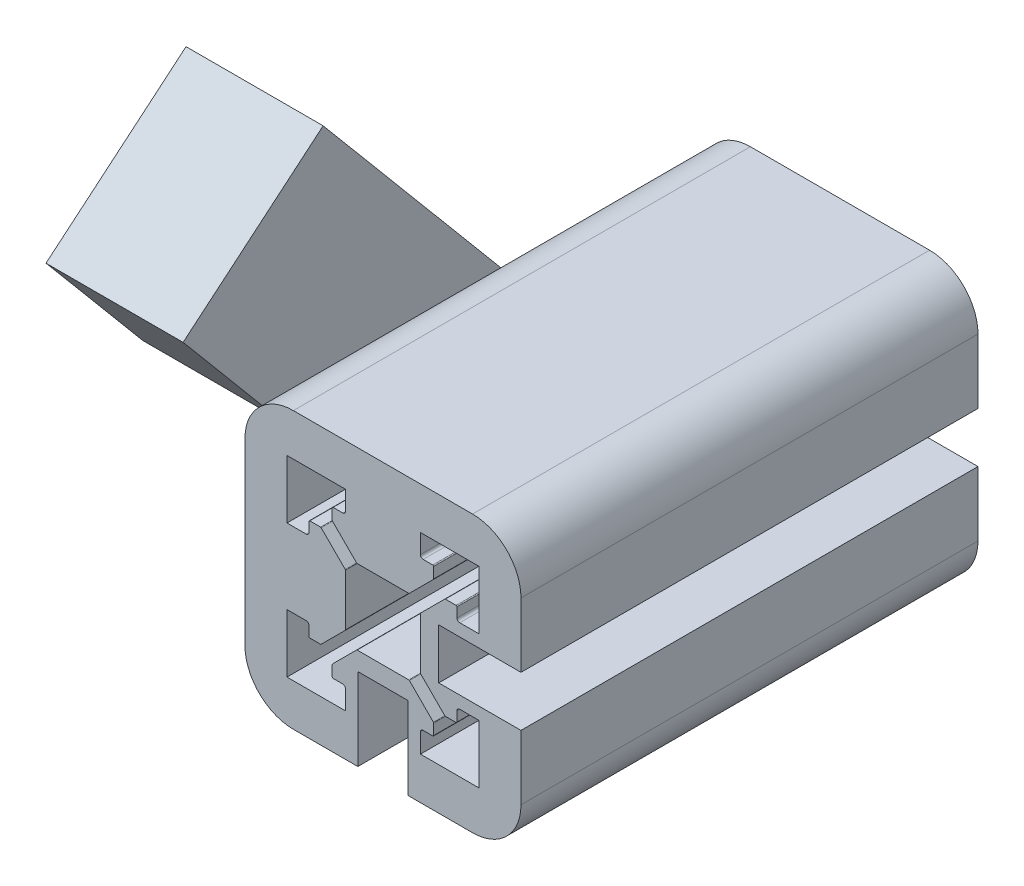
SolidWorks part; units mm, degrees
ref_plane "Ön Düzlem" through (0, 0, 0) normal (0, 0, 1) x (1, 0, 0)
ref_plane "Üst Düzlem" through (0, 0, 0) normal (0, 1, 0) x (1, 0, 0)
ref_plane "Sağ Düzlem" through (0, 0, 0) normal (1, 0, 0) x (0, 0, -1)
sketch "Çizim6" plane through (0, 0, 0) normal (0, 0, 1) x (1, 0, 0)
  line L5 (-115.3715, 18.9738) -> (-110.3715, 18.9738)
  line L6 (-115.3715, 13.4738) -> (-110.3715, 13.4738)
  line L64 (-135.0715, 20.3238) -> (-133.8715, 20.3238)
  line L65 (-133.5715, 20.6238) -> (-133.5715, 21.6738)
  line L66 (-133.4715, 21.7738) -> (-132.3044, 21.7738)
  line L67 (-132.2336, 21.7445) -> (-129.6008, 19.1116)
  line L68 (-129.5715, 19.0409) -> (-129.5715, 13.4066)
  line L69 (-132.2336, 10.7031) -> (-129.6008, 13.3359)
  line L70 (-133.4715, 10.6738) -> (-132.3044, 10.6738)
  line L71 (-133.5715, 11.8238) -> (-133.5715, 10.7738)
  line L72 (-135.0715, 12.1238) -> (-133.8715, 12.1238)
  line L79 (-129.5715, 6.6238) -> (-129.5715, 7.8238)
  line L80 (-129.8715, 8.1238) -> (-130.9215, 8.1238)
  line L81 (-131.0215, 8.2238) -> (-131.0215, 9.3909)
  line L82 (-130.9922, 9.4616) -> (-128.3594, 12.0945)
  line L83 (-128.2887, 12.1238) -> (-122.6544, 12.1238)
  line L84 (-119.9508, 9.4616) -> (-122.5836, 12.0945)
  line L85 (-119.9215, 8.2238) -> (-119.9215, 9.3909)
  line L86 (-121.0715, 8.1238) -> (-120.0215, 8.1238)
  line L87 (-121.3715, 6.6238) -> (-121.3715, 7.8238)
  line L94 (-115.8715, 12.1238) -> (-117.0715, 12.1238)
  line L95 (-117.3715, 11.8238) -> (-117.3715, 10.7738)
  line L96 (-117.4715, 10.6738) -> (-118.6387, 10.6738)
  line L97 (-118.7094, 10.7031) -> (-121.3422, 13.3359)
  line L98 (-121.3715, 13.4066) -> (-121.3715, 19.0409)
  line L99 (-118.7094, 21.7445) -> (-121.3422, 19.1116)
  line L100 (-117.4715, 21.7738) -> (-118.6387, 21.7738)
  line L101 (-117.3715, 20.6238) -> (-117.3715, 21.6738)
  line L102 (-115.8715, 20.3238) -> (-117.0715, 20.3238)
  line L109 (-121.3715, 25.8238) -> (-121.3715, 24.6238)
  line L110 (-121.0715, 24.3238) -> (-120.0215, 24.3238)
  line L111 (-119.9215, 24.2238) -> (-119.9215, 23.0566)
  line L112 (-119.9508, 22.9859) -> (-122.5836, 20.3531)
  line L113 (-122.6544, 20.3238) -> (-128.2887, 20.3238)
  line L114 (-130.9922, 22.9859) -> (-128.3594, 20.3531)
  line L115 (-131.0215, 24.2238) -> (-131.0215, 23.0566)
  line L116 (-129.8715, 24.3238) -> (-130.9215, 24.3238)
  line L117 (-129.5715, 25.8238) -> (-129.5715, 24.6238)
  line L122 (-119.3715, 18.9738) -> (-115.3715, 18.9738)
  line L123 (-119.3715, 13.4738) -> (-115.3715, 13.4738)
  line L126 (-119.3715, 18.9738) -> (-119.3715, 13.4738)
  line L128 (-122.7215, 10.1238) -> (-122.7215, 6.1238)
  line L129 (-122.7215, 10.1238) -> (-128.2215, 10.1238)
  line L130 (-128.2215, 10.1238) -> (-128.2215, 6.1238)
  line L142 (-135.0715, 20.3238) -> (-135.8715, 20.3238)
  line L143 (-135.0715, 12.1238) -> (-135.5715, 12.1238)
  line L144 (-129.5715, 6.6238) -> (-129.5715, 6.1238)
  line L145 (-129.5715, 25.8238) -> (-129.5715, 26.6238)
  line L146 (-121.3715, 25.8238) -> (-121.3715, 26.3238)
  line L147 (-115.8715, 20.3238) -> (-115.3715, 20.3238)
  line L148 (-115.8715, 12.1238) -> (-115.3715, 12.1238)
  line L149 (-121.3715, 6.6238) -> (-121.3715, 6.1238)
  line L150 (-135.2715, 31.3238) -> (-130.0215, 31.3238)
  line L151 (-130.0215, 31.3238) -> (-128.2215, 31.3238)
  line L152 (-125.4715, 31.3238) -> (-125.4715, 31.3238)
  line L153 (-125.4715, 31.3238) -> (-125.4715, 31.3238)
  line L154 (-125.4715, 31.3238) -> (-125.4715, 31.3238)
  line L155 (-120.9215, 31.3238) -> (-122.7215, 31.3238)
  line L156 (-120.9215, 31.3238) -> (-115.6715, 31.3238)
  line L157 (-110.3715, 20.7738) -> (-110.3715, 26.0238)
  line L158 (-110.3715, 20.7738) -> (-110.3715, 18.9738)
  line L159 (-110.3715, 16.2238) -> (-110.3715, 16.2238)
  line L160 (-110.3715, 16.2238) -> (-110.3715, 16.2238)
  line L161 (-110.3715, 16.2238) -> (-110.3715, 16.2238)
  line L162 (-110.3715, 11.6738) -> (-110.3715, 13.4738)
  line L163 (-110.3715, 6.4238) -> (-110.3715, 11.6738)
  line L164 (-120.9215, 1.1238) -> (-115.6715, 1.1238)
  line L165 (-120.9215, 1.1238) -> (-122.7215, 1.1238)
  line L166 (-125.4715, 1.1238) -> (-125.4715, 1.1238)
  line L167 (-125.4715, 1.1238) -> (-125.4715, 1.1238)
  line L168 (-125.4715, 1.1238) -> (-125.4715, 1.1238)
  line L169 (-130.0215, 1.1238) -> (-128.2215, 1.1238)
  line L170 (-135.2715, 1.1238) -> (-130.0215, 1.1238)
  line L171 (-140.5715, 6.4238) -> (-140.5715, 11.6738)
  line L172 (-140.5715, 11.6738) -> (-140.5715, 16.2238)
  line L173 (-140.5715, 16.2238) -> (-140.5715, 16.2238)
  line L174 (-140.5715, 16.2238) -> (-140.5715, 16.2238)
  line L175 (-140.5715, 16.2238) -> (-140.5715, 16.2238)
  line L176 (-140.5715, 20.7738) -> (-140.5715, 16.2238)
  line L177 (-140.5715, 20.7738) -> (-140.5715, 26.0238)
  line L178 (-135.5715, 20.7738) -> (-135.5715, 26.0238) construction
  line L179 (-135.2715, 26.3238) -> (-130.0215, 26.3238) construction
  line L180 (-115.3715, 20.7738) -> (-115.3715, 26.0238) construction
  line L181 (-120.9215, 26.3238) -> (-115.6715, 26.3238) construction
  line L182 (-115.3715, 20.7738) -> (-115.3715, 18.9738) construction
  line L183 (-115.3715, 6.4238) -> (-115.3715, 11.6738) construction
  line L184 (-120.9215, 6.1238) -> (-115.6715, 6.1238) construction
  line L185 (-115.3715, 11.6738) -> (-115.3715, 13.4738) construction
  line L186 (-120.9215, 6.1238) -> (-122.7215, 6.1238) construction
  line L187 (-120.9215, 26.3238) -> (-122.7215, 26.3238) construction
  line L188 (-130.0215, 26.3238) -> (-128.2215, 26.3238) construction
  line L189 (-135.5715, 20.7738) -> (-135.5715, 18.9738) construction
  line L190 (-135.5715, 11.6738) -> (-135.5715, 13.4738) construction
  line L191 (-135.5715, 6.4238) -> (-135.5715, 11.6738) construction
  line L192 (-135.2715, 6.1238) -> (-130.0215, 6.1238) construction
  line L193 (-130.0215, 6.1238) -> (-128.2215, 6.1238) construction
  line L194 (-122.7215, 6.1238) -> (-122.7215, 1.1238)
  line L195 (-128.2215, 6.1238) -> (-128.2215, 1.1238)
  line L196 (-135.8715, 20.3238) -> (-135.9715, 20.3238)
  line L197 (-135.9715, 20.2238) -> (-135.9715, 26.7238) construction
  line L198 (-122.7215, 31.3238) -> (-128.2215, 31.3238)
  line L204 (-110.3715, 20.7738) -> (-110.3715, 16.2238) construction
  line L205 (-110.3715, 11.6738) -> (-110.3715, 16.2238) construction
  line L206 (-120.9215, 31.3238) -> (-125.4715, 31.3238) construction
  line L207 (-130.0215, 31.3238) -> (-125.4715, 31.3238) construction
  line L208 (-120.9215, 1.1238) -> (-125.4715, 1.1238) construction
  line L209 (-130.0215, 1.1238) -> (-125.4715, 1.1238) construction
  line L210 (-131.5715, 13.4738) -> (-135.5715, 13.4738) [skipped]
  line L211 (-131.5715, 13.4738) -> (-135.5715, 13.4738) construction
  line L212 (-131.5715, 13.4738) -> (-131.5715, 18.9738) [skipped]
  line L213 (-131.5715, 13.4738) -> (-131.5715, 18.9738) construction
  line L214 (-131.5715, 18.9738) -> (-135.5715, 18.9738) [skipped]
  line L215 (-131.5715, 18.9738) -> (-135.5715, 18.9738) construction
  line L216 (-129.5715, 26.6238) -> (-129.5715, 26.7238)
  line L217 (-135.9715, 26.7238) -> (-129.4715, 26.7238) construction
  line L218 (-114.9715, 26.7238) -> (-114.9715, 20.3238)
  line L219 (-121.3715, 26.7238) -> (-114.9715, 26.7238)
  line L220 (-114.9715, 5.7238) -> (-121.3715, 5.7238)
  line L221 (-114.9715, 12.1238) -> (-114.9715, 5.7238)
  line L222 (-135.9715, 5.7238) -> (-135.9715, 12.1238)
  line L223 (-129.5715, 5.7238) -> (-135.9715, 5.7238)
  line L224 (-121.3715, 6.1238) -> (-121.3715, 5.7238)
  line L225 (-115.3715, 12.1238) -> (-114.9715, 12.1238)
  line L226 (-129.5715, 6.1238) -> (-129.5715, 5.7238)
  line L227 (-135.9715, 20.3238) -> (-135.9715, 26.7238)
  line L228 (-135.9715, 26.7238) -> (-129.5715, 26.7238)
  line L229 (-135.5715, 12.1238) -> (-135.9715, 12.1238)
  line L230 (-121.3715, 26.3238) -> (-121.3715, 26.7238)
  line L231 (-115.3715, 20.3238) -> (-114.9715, 20.3238)
  line L240 (-121.4715, 25.8238) -> (-121.4715, 26.3238) construction
  line L241 (-121.4715, 25.8238) -> (-121.4715, 24.6238) construction
  line L242 (-121.0715, 24.2238) -> (-120.0215, 24.2238) construction
  line L243 (-120.0215, 24.2238) -> (-120.0215, 23.0566) construction
  line L244 (-120.0215, 23.0566) -> (-122.6544, 20.4238) construction
  line L245 (-122.6544, 20.4238) -> (-128.2887, 20.4238) construction
  line L246 (-130.9215, 23.0566) -> (-128.2887, 20.4238) construction
  line L247 (-130.9215, 24.2238) -> (-130.9215, 23.0566) construction
  line L248 (-129.8715, 24.2238) -> (-130.9215, 24.2238) construction
  line L249 (-129.4715, 25.8238) -> (-129.4715, 24.6238) construction
  line L250 (-129.4715, 25.8238) -> (-129.4715, 26.7238) construction
  line L251 (-135.8715, 26.6238) -> (-129.5715, 26.6238) construction
  line L252 (-135.8715, 20.3238) -> (-135.8715, 26.6238) construction
  line L253 (-135.0715, 20.2238) -> (-135.9715, 20.2238) construction
  line L254 (-135.0715, 20.2238) -> (-133.8715, 20.2238) construction
  line L255 (-133.4715, 20.6238) -> (-133.4715, 21.6738) construction
  line L256 (-133.4715, 21.6738) -> (-132.3044, 21.6738) construction
  line L257 (-132.3044, 21.6738) -> (-129.6715, 19.0409) construction
  line L258 (-129.6715, 19.0409) -> (-129.6715, 13.4066) construction
  line L259 (-132.3044, 10.7738) -> (-129.6715, 13.4066) construction
  line L260 (-133.4715, 10.7738) -> (-132.3044, 10.7738) construction
  line L261 (-133.4715, 11.8238) -> (-133.4715, 10.7738) construction
  line L262 (-135.0715, 12.2238) -> (-133.8715, 12.2238) construction
  line L263 (-135.0715, 12.2238) -> (-135.5715, 12.2238) construction
  line L264 (-128.2215, 22.3238) -> (-128.2215, 26.3238) [skipped]
  line L265 (-128.2215, 22.3238) -> (-128.2215, 26.3238) construction
  line L266 (-128.2215, 22.3238) -> (-122.7215, 22.3238) [skipped]
  line L267 (-128.2215, 22.3238) -> (-122.7215, 22.3238) construction
  line L268 (-122.7215, 22.3238) -> (-122.7215, 26.3238) [skipped]
  line L269 (-122.7215, 22.3238) -> (-122.7215, 26.3238) construction
  arc A46 (-133.8715, 20.3238) -> (-133.5715, 20.6238) centre (-133.8715, 20.6238) ccw
  arc A47 (-133.5715, 21.6738) -> (-133.4715, 21.7738) centre (-133.4715, 21.6738) cw
  arc A48 (-132.2336, 21.7445) -> (-132.3044, 21.7738) centre (-132.3044, 21.6738) ccw
  arc A49 (-129.5715, 19.0409) -> (-129.6008, 19.1116) centre (-129.6715, 19.0409) ccw
  arc A50 (-129.5715, 13.4066) -> (-129.6008, 13.3359) centre (-129.6715, 13.4066) cw
  arc A51 (-132.2336, 10.7031) -> (-132.3044, 10.6738) centre (-132.3044, 10.7738) cw
  arc A52 (-133.4715, 10.6738) -> (-133.5715, 10.7738) centre (-133.4715, 10.7738) cw
  arc A53 (-133.5715, 11.8238) -> (-133.8715, 12.1238) centre (-133.8715, 11.8238) ccw
  arc A57 (-129.5715, 7.8238) -> (-129.8715, 8.1238) centre (-129.8715, 7.8238) ccw
  arc A58 (-130.9215, 8.1238) -> (-131.0215, 8.2238) centre (-130.9215, 8.2238) cw
  arc A59 (-130.9922, 9.4616) -> (-131.0215, 9.3909) centre (-130.9215, 9.3909) ccw
  arc A60 (-128.2887, 12.1238) -> (-128.3594, 12.0945) centre (-128.2887, 12.0238) ccw
  arc A61 (-122.6544, 12.1238) -> (-122.5836, 12.0945) centre (-122.6544, 12.0238) cw
  arc A62 (-119.9508, 9.4616) -> (-119.9215, 9.3909) centre (-120.0215, 9.3909) cw
  arc A63 (-119.9215, 8.2238) -> (-120.0215, 8.1238) centre (-120.0215, 8.2238) cw
  arc A64 (-121.0715, 8.1238) -> (-121.3715, 7.8238) centre (-121.0715, 7.8238) ccw
  arc A68 (-117.0715, 12.1238) -> (-117.3715, 11.8238) centre (-117.0715, 11.8238) ccw
  arc A69 (-117.3715, 10.7738) -> (-117.4715, 10.6738) centre (-117.4715, 10.7738) cw
  arc A70 (-118.7094, 10.7031) -> (-118.6387, 10.6738) centre (-118.6387, 10.7738) ccw
  arc A71 (-121.3715, 13.4066) -> (-121.3422, 13.3359) centre (-121.2715, 13.4066) ccw
  arc A72 (-121.3715, 19.0409) -> (-121.3422, 19.1116) centre (-121.2715, 19.0409) cw
  arc A73 (-118.7094, 21.7445) -> (-118.6387, 21.7738) centre (-118.6387, 21.6738) cw
  arc A74 (-117.4715, 21.7738) -> (-117.3715, 21.6738) centre (-117.4715, 21.6738) cw
  arc A75 (-117.3715, 20.6238) -> (-117.0715, 20.3238) centre (-117.0715, 20.6238) ccw
  arc A79 (-121.3715, 24.6238) -> (-121.0715, 24.3238) centre (-121.0715, 24.6238) ccw
  arc A80 (-120.0215, 24.3238) -> (-119.9215, 24.2238) centre (-120.0215, 24.2238) cw
  arc A81 (-119.9508, 22.9859) -> (-119.9215, 23.0566) centre (-120.0215, 23.0566) ccw
  arc A82 (-122.6544, 20.3238) -> (-122.5836, 20.3531) centre (-122.6544, 20.4238) ccw
  arc A83 (-128.2887, 20.3238) -> (-128.3594, 20.3531) centre (-128.2887, 20.4238) cw
  arc A84 (-130.9922, 22.9859) -> (-131.0215, 23.0566) centre (-130.9215, 23.0566) cw
  arc A85 (-131.0215, 24.2238) -> (-130.9215, 24.3238) centre (-130.9215, 24.2238) cw
  arc A86 (-129.8715, 24.3238) -> (-129.5715, 24.6238) centre (-129.8715, 24.6238) ccw
  arc A89 (-110.3715, 26.0238) -> (-115.6715, 31.3238) centre (-115.6715, 26.0238) ccw
  arc A90 (-115.6715, 1.1238) -> (-110.3715, 6.4238) centre (-115.6715, 6.4238) ccw
  arc A91 (-135.2715, 1.1238) -> (-140.5715, 6.4238) centre (-135.2715, 6.4238) cw
  arc A92 (-140.5715, 26.0238) -> (-135.2715, 31.3238) centre (-135.2715, 26.0238) cw
  arc A93 (-135.5715, 26.0238) -> (-135.2715, 26.3238) centre (-135.2715, 26.0238) cw construction
  arc A94 (-115.3715, 26.0238) -> (-115.6715, 26.3238) centre (-115.6715, 26.0238) ccw construction
  arc A95 (-115.6715, 6.1238) -> (-115.3715, 6.4238) centre (-115.6715, 6.4238) ccw construction
  arc A96 (-135.2715, 6.1238) -> (-135.5715, 6.4238) centre (-135.2715, 6.4238) cw construction
  arc A98 (-133.4715, 10.7738) -> (-133.4715, 10.7738) centre (-133.4715, 10.7738) cw
  arc A99 (-132.3044, 10.7738) -> (-132.3044, 10.7738) centre (-132.3044, 10.7738) cw
  arc A100 (-129.6715, 13.4066) -> (-129.6715, 13.4066) centre (-129.6715, 13.4066) cw
  arc A101 (-129.6715, 19.0409) -> (-129.6715, 19.0409) centre (-129.6715, 19.0409) ccw
  arc A102 (-132.3044, 21.6738) -> (-132.3044, 21.6738) centre (-132.3044, 21.6738) ccw
  arc A103 (-133.4715, 21.6738) -> (-133.4715, 21.6738) centre (-133.4715, 21.6738) cw
  arc A106 (-130.9215, 24.2238) -> (-130.9215, 24.2238) centre (-130.9215, 24.2238) cw
  arc A107 (-130.9215, 23.0566) -> (-130.9215, 23.0566) centre (-130.9215, 23.0566) cw
  arc A108 (-128.2887, 20.4238) -> (-128.2887, 20.4238) centre (-128.2887, 20.4238) cw
  arc A109 (-122.6544, 20.4238) -> (-122.6544, 20.4238) centre (-122.6544, 20.4238) ccw
  arc A110 (-120.0215, 23.0566) -> (-120.0215, 23.0566) centre (-120.0215, 23.0566) ccw
  arc A111 (-120.0215, 24.2238) -> (-120.0215, 24.2238) centre (-120.0215, 24.2238) cw
  arc A113 (-121.4715, 24.6238) -> (-121.0715, 24.2238) centre (-121.0715, 24.6238) ccw construction
  arc A114 (-129.8715, 24.2238) -> (-129.4715, 24.6238) centre (-129.8715, 24.6238) ccw construction
  arc A115 (-133.8715, 20.2238) -> (-133.4715, 20.6238) centre (-133.8715, 20.6238) ccw construction
  arc A116 (-133.4715, 11.8238) -> (-133.8715, 12.2238) centre (-133.8715, 11.8238) ccw construction
  point P0 (-125.4715, 16.2238)
  point P123 (-125.4715, 16.2238)
  point P329 (-125.4715, 16.2238)
  dimension "D6" = 4
  dimension "D2" = 0.1
  dimension "D3" = 5
  dimension "D4" = 2.4
  dimension "D5" = 2.4
  dimension "D14" = 4
extrude "Yükseklik-Ekstrüzyon3" add sketch "Çizim6" along normal mid plane 50
sketch "Çizim8" plane through (-140.5715, 0, 0) normal (-1, 0, 0) x (0, 0, 1)
  line L0 (0, 0) -> (0, 36.5333) construction
  line L2 (23.2295, 43.9076) -> (-24.1045, -12.5029) construction
  line L3 (16.4441, 51.3783) -> (-31.765, -6.075)
  line L4 (16.4441, 51.3783) -> (31.765, 38.5226)
  line L9 (-31.765, -6.075) -> (-16.4441, -18.9308)
  line L10 (31.765, 38.5226) -> (-16.4441, -18.9308)
  line L11 (16.4441, 51.3783) -> (-16.4441, -18.9308) construction
  line L12 (-31.765, -6.075) -> (31.765, 38.5226) construction
  line L13 (25, 6.4238) -> (25, 26.0238) construction
  point P4 (0, 0)
  point P6 (0, 16.2238)
  point P7 (24.1045, 44.9504)
  point P9 (25, 16.2238)
  point P14 (0, 0)
  point P16 (-24.1045, -12.5029)
  line M12 (-25, 6.4238) -> (25, 6.4238)
  line M14 (25, 26.0238) -> (-25, 26.0238)
  dimension "D1" = 40
  dimension "D2" = 75
  dimension "D3" = 20
extrude "Yükseklik-Ekstrüzyon4" add sketch "Çizim8" along normal blind 15 contours L10 L3 L9 M12 | L10 L3 M14 M12 | L10 L4 L3 M14
sketch "Çizim11" plane through (-155.5715, 0, 0) normal (-1, 0, 0) x (0, 0, 1)
  line L0 (24.1045, 44.9504) -> (-24.1045, -12.5029) construction
  line L1 (16.4441, 51.3783) -> (31.765, 38.5226) construction
  line L2 (-31.765, -6.075) -> (-16.4441, -18.9308) construction
  circle A1 centre (17.9981, 37.673) radius 3.5
  circle A2 centre (-17.9981, -5.2255) radius 3.5
  point P12 (0, 16.2238)
  dimension "D1" = 56
  dimension "D3" = 7
  dimension "D2" = 28
extrude "Kes-Ekstrüzyon3" cut sketch "Çizim11" against normal blind 10 contours A2 | A1
sketch "Çizim12" plane through (0, 13.1311, -15.6491) normal (0, 0.6428, -0.766) x (1, 0, 0)
  line L0 (-155.5715, 22.3702) -> (-155.5715, 25.0719)
  line L1 (-153.5715, 23.0719) -> (-153.5715, 23.0719)
  line L2 (-153.5715, 23.0719) -> (-153.5715, 23.0719)
  line L3 (-153.5715, 23.0719) -> (-153.5715, -47.9281)
  line L4 (-153.5715, -47.9281) -> (-142.5715, -47.9281)
  line L5 (-142.5715, -47.9281) -> (-142.5715, -16.8301)
  line L6 (-142.5715, -16.8301) -> (-142.5715, 8.7559)
  line L7 (-142.5715, 8.7559) -> (-142.5715, 23.0719)
  line L8 (-142.5715, 23.0719) -> (-153.5715, 23.0719)
  line L12 (-155.5715, 25.0719) -> (-155.5715, -49.9281)
  line L13 (-155.5715, -49.9281) -> (-140.5715, -49.9281)
  line L14 (-140.5715, -49.9281) -> (-140.5715, -16.8301)
  line L15 (-140.5715, -16.8301) -> (-140.5715, 8.7559)
  line L16 (-140.5715, 8.7559) -> (-140.5715, 25.0719)
  line L17 (-140.5715, 25.0719) -> (-155.5715, 25.0719)
  line L22 (-155.5715, 25.0719) -> (-155.5715, -49.9281)
  line L23 (-155.5715, -49.9281) -> (-140.5715, -49.9281)
  line L24 (-140.5715, -49.9281) -> (-140.5715, -16.8301)
  line L25 (-140.5715, -16.8301) -> (-140.5715, 8.7559)
  line L26 (-140.5715, 8.7559) -> (-140.5715, 25.0719)
  line L27 (-140.5715, 25.0719) -> (-155.5715, 25.0719)
  line L39 (-155.5715, 25.0719) -> (-155.5715, 22.3702) construction
  dimension "D1" = 0
  dimension "D2" = 2
extrude "Kes-Ekstrüzyon4" cut sketch "Çizim12" against normal blind 16
sketch "Çizim13" plane through (-155.5715, 0, 0) normal (-1, 0, 0) x (0, 0, 1)
  line L10 (-5.8381, -6.291) -> (-21.159, 6.5647)
  line L11 (21.159, 25.8828) -> (5.8381, 38.7386)
  line L19 (-16.4441, -18.9308) -> (31.765, 38.5226)
  line L20 (31.765, 38.5226) -> (16.4441, 51.3783)
  line L21 (16.4441, 51.3783) -> (-31.765, -6.075)
  line L22 (-31.765, -6.075) -> (-16.4441, -18.9308)
  line L23 (-16.4441, -18.9308) -> (31.765, 38.5226)
  line L24 (31.765, 38.5226) -> (16.4441, 51.3783)
  line L25 (16.4441, 51.3783) -> (-31.765, -6.075)
  line L26 (-31.765, -6.075) -> (-16.4441, -18.9308)
  point P8 (-7.6604, 22.6516)
  dimension "D1" = 0
  dimension "D2" = 42
  dimension "D3" = 21
extrude "Kes-Ekstrüzyon5" cut sketch "Çizim13" against normal up to surface (13 mm away)
